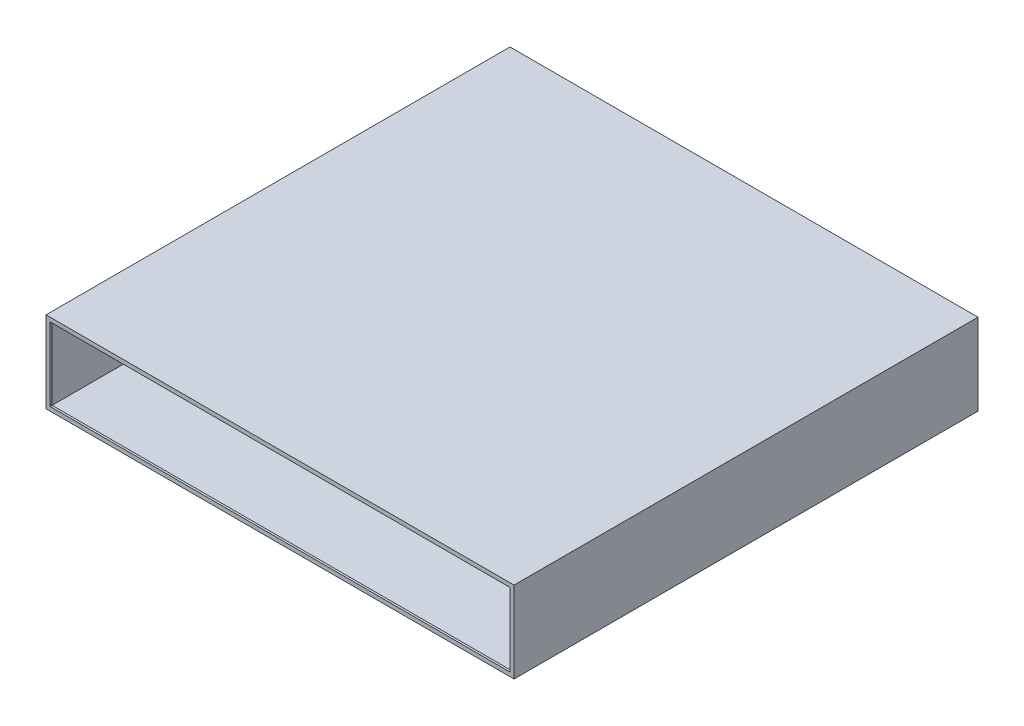
SolidWorks part; units mm, degrees
material "Окись алюминия"
ref_plane "Спереди" through (0, 0, 0) normal (0, 0, 1) x (1, 0, 0)
ref_plane "Сверху" through (0, 0, 0) normal (0, 1, 0) x (1, 0, 0)
ref_plane "Справа" through (0, 0, 0) normal (1, 0, 0) x (0, 0, -1)
sketch "Эскиз1" plane through (0, 0, 0) normal (0, 0, 1) x (1, 0, 0)
  line L1 (-228.6, 38.1) -> (228.6, 38.1)
  line L2 (-228.6, 38.1) -> (-228.6, -38.1)
  line L3 (-228.6, -38.1) -> (228.6, -38.1)
  line L4 (228.6, 38.1) -> (228.6, -38.1)
  line L5 (-228.6, 38.1) -> (228.6, -38.1) construction
  line L6 (-228.6, -38.1) -> (228.6, 38.1) construction
  point P0 (0, 0)
  dimension "D1" = 457.2
  dimension "D2" = 76.2
extrude "Вытянуть-Тонкостенный1" add sketch "Эскиз1" along normal blind 457.2 thin thin type one direction wall 2
sketch "Эскиз2" plane through (0, 0, 457.2) normal (0, 0, 1) x (1, 0, 0)
  line L0 (-226.6, 36.1) -> (-226.6, -36.1)
  line L1 (-230.6, 40.1) -> (230.6, 40.1)
  line L2 (-230.6, 40.1) -> (-230.6, -40.1)
  line L3 (-230.6, -40.1) -> (230.6, -40.1)
  line L4 (230.6, 40.1) -> (230.6, -40.1)
  line L5 (-226.6, -36.1) -> (226.6, -36.1)
  line L6 (226.6, 36.1) -> (226.6, -36.1)
  line L7 (-226.6, 36.1) -> (226.6, 36.1)
  dimension "D1" = 4
extrude "Бобышка-Вытянуть1" add sketch "Эскиз2" against normal blind 2
